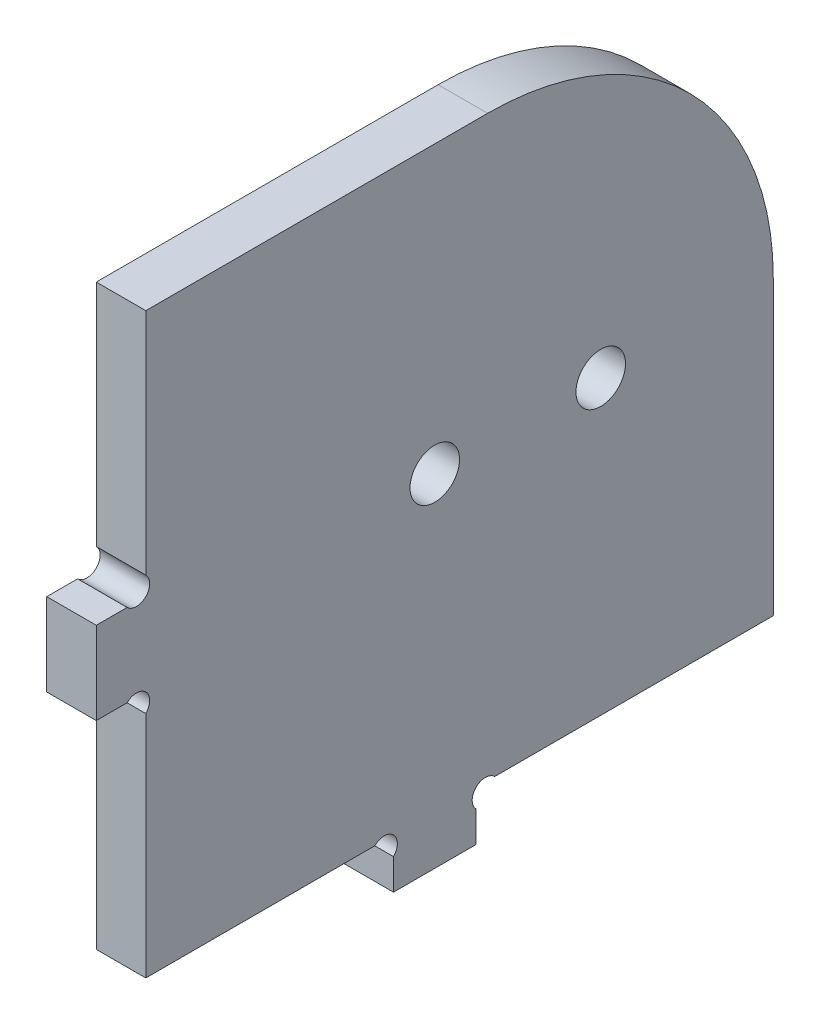
SolidWorks part; units mm, degrees
ref_plane "Plan de face" through (0, 0, 0) normal (0, 0, 1) x (1, 0, 0)
ref_plane "Plan de dessus" through (0, 0, 0) normal (0, 1, 0) x (1, 0, 0)
ref_plane "Plan de droite" through (0, 0, 0) normal (1, 0, 0) x (0, 0, -1)
sketch "Esquisse1" plane through (0, 0, 0) normal (1, 0, 0) x (0, 0, -1)
  line L0 (0, -4.5625) -> (0, 134.1836) construction
  line L1 (-32.3115, 0) -> (104.4265, 0) construction
  line L2 (-24.3695, 6) -> (94.833, 6) construction
  line L3 (6, -26.2376) -> (6, 112.02) construction
  line L4 (82, -26.2376) -> (82, 134.1836) construction
  line L5 (-26.3115, 76) -> (110.4265, 76) construction
  line L6 (41, 99.8569) -> (41, -16.9546) construction
  line L7 (94.833, 41.4) -> (32.7277, 41.4) construction
  line L8 (46, 9.2963) -> (46, -16.9546) construction
  line L9 (-8.4142, 41) -> (14.8973, 41) construction
  line L10 (-8.4142, 36) -> (14.8973, 36) construction
  line L11 (6, 36) -> (-7.6399, 22.3601) construction
  line L12 (46, 3.7373) -> (46, 0)
  line L13 (46, 6) -> (62.0517, -10.0517) construction
  line L14 (46, 0) -> (36, 0)
  line L15 (36, 0) -> (36, 3.7373)
  line L16 (3.7373, 36) -> (0, 36)
  line L17 (0, 36) -> (0, 46)
  line L18 (0, 46) -> (3.7373, 46)
  line L19 (33.7373, 6) -> (6, 6)
  line L20 (6, 6) -> (6, 33.7373)
  line L21 (6, 48.2627) -> (6, 76)
  line L22 (6, 76) -> (47.4, 76)
  line L23 (82, 41.4) -> (82, 6)
  line L24 (82, 6) -> (48.2627, 6)
  line L25 (47.4, 89.1717) -> (47.4, 36) construction
  line L28 (41, 41.4) -> (76.7902, 62.0635) construction
  line L29 (41, 41.4) -> (61.9968, 5.0325) construction
  circle A0 centre (41, 41.4) radius 3
  arc A1 (48.2627, 6) -> (46, 3.7373) centre (47.1314, 4.8686) ccw
  arc A2 (33.7373, 6) -> (36, 3.7373) centre (34.8686, 4.8686) cw
  arc A3 (6, 33.7373) -> (3.7373, 36) centre (4.8686, 34.8686) ccw
  arc A4 (6, 48.2627) -> (3.7373, 46) centre (4.8686, 47.1314) cw
  circle A5 centre (61.1, 41.4) radius 15.1 construction
  arc A6 (82, 41.4) -> (47.4, 76) centre (47.4, 41.4) ccw
  circle A7 centre (61.1, 41.4) radius 3
  circle A9 centre (41, 41.4) radius 5 construction
  dimension "D7" = 35
  dimension "D12" = 34.6
  dimension "D14" = 60
  dimension "D3" = 90
  dimension "D1" = 6
  dimension "D2" = 6
  dimension "D4" = 76
  dimension "D5" = 41
  dimension "D6" = 35.4
  dimension "D8" = 5
  dimension "D9" = 45
  dimension "D10" = 5
  dimension "D11" = 45
extrude "Boss.-Extru.1" add sketch "Esquisse1" along normal blind 6
